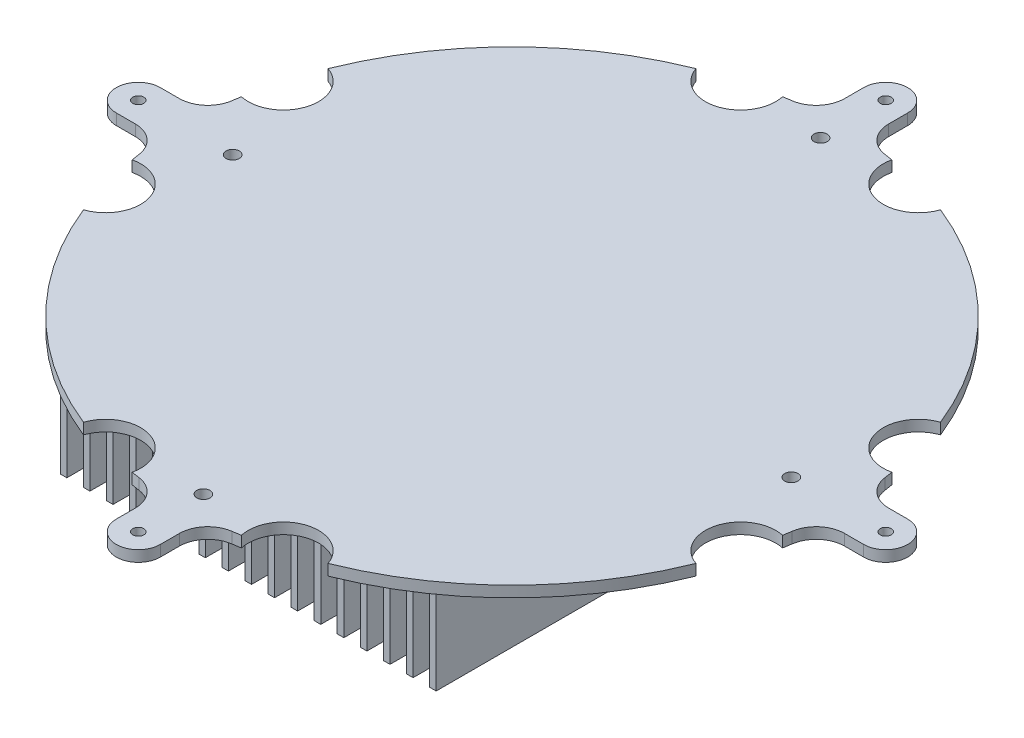
SolidWorks part; units mm, degrees
material "1060 Alloy"
ref_plane "Front Plane" through (0, 0, 0) normal (0, 0, 1) x (1, 0, 0)
ref_plane "Top Plane" through (0, 0, 0) normal (0, 1, 0) x (1, 0, 0)
ref_plane "Right Plane" through (0, 0, 0) normal (1, 0, 0) x (0, 0, -1)
sketch "Sketch3" plane through (0, 0, 0) normal (0, 1, 0) x (1, 0, 0)
  line L0 (0, 0) -> (211.9111, 0) construction
  line L1 (0, 0) -> (-205.2426, 0) construction
  line L2 (0, 0) -> (0, 170) construction
  line L3 (0, 0) -> (0, -200) construction
  line L4 (161.3691, 10) -> (170, 10)
  line L5 (161.3691, -10) -> (170, -10)
  line L6 (-10, 161.3691) -> (-10, 170)
  line L7 (10, 161.3691) -> (10, 170)
  line L8 (10, -161.3691) -> (10, -170)
  line L9 (-10, -161.3691) -> (-10, -170)
  line L10 (-161.3691, -10) -> (-170, -10)
  line L11 (-161.3691, 10) -> (-170, 10)
  arc A0 (-21.1656, 148.4992) -> (-148.4992, 21.1656) centre (0, 0) ccw
  circle A1 centre (0, 170) radius 2.5
  arc A2 (-10, 170) -> (10, 170) centre (0, 170) cw
  arc A3 (10, 161.3691) -> (21.1656, 148.4992) centre (23, 161.3691) ccw
  arc A4 (-10, 161.3691) -> (-21.1656, 148.4992) centre (-23, 161.3691) cw
  arc A5 (170, 10) -> (170, -10) centre (170, 0) cw
  arc A6 (161.3691, 10) -> (148.4992, 21.1656) centre (161.3691, 23) cw
  circle A7 centre (170, 0) radius 2.5
  arc A8 (161.3691, -10) -> (148.4992, -21.1656) centre (161.3691, -23) ccw
  arc A9 (10, -170) -> (-10, -170) centre (0, -170) cw
  arc A10 (10, -161.3691) -> (21.1656, -148.4992) centre (23, -161.3691) cw
  circle A11 centre (0, -170) radius 2.5
  arc A12 (-10, -161.3691) -> (-21.1656, -148.4992) centre (-23, -161.3691) ccw
  arc A13 (-170, -10) -> (-170, 10) centre (-170, 0) cw
  arc A14 (-161.3691, -10) -> (-148.4992, -21.1656) centre (-161.3691, -23) cw
  circle A15 centre (-170, 0) radius 2.5
  arc A16 (-161.3691, 10) -> (-148.4992, 21.1656) centre (-161.3691, 23) ccw
  arc A17 (-148.4992, -21.1656) -> (-21.1656, -148.4992) centre (0, 0) ccw
  arc A18 (148.4992, 21.1656) -> (21.1656, 148.4992) centre (0, 0) ccw
  arc A19 (21.1656, -148.4992) -> (148.4992, -21.1656) centre (0, 0) ccw
  point P53 (0, 0)
  dimension "D1" = 300
  dimension "D4" = 5
  dimension "D2" = 4
extrude "Boss-Extrude4" add sketch "Sketch3" against normal blind 5
sketch "Sketch4" plane through (0, -5, 0) normal (0, -1, 0) x (1, 0, 0)
  line L0 (0, 0) -> (0, -192.7937) construction
  line L1 (0, 0) -> (0, 216.5128) construction
  line L2 (0, 0) -> (-235.9747, 0) construction
  line L3 (0, 0) -> (242.3846, 0) construction
  line L4 (1.5, -120) -> (-1.5, -120)
  line L5 (1.5, -120) -> (1.5, 120)
  line L6 (-1.5, -120) -> (-1.5, 120)
  line L7 (1.5, 120) -> (-1.5, 120)
  line L8 (12, -120) -> (12, 120)
  line L9 (9, -120) -> (9, 120)
  line L10 (12, 120) -> (9, 120)
  line L11 (12, -120) -> (9, -120)
  line L12 (22.5, -120) -> (22.5, 120)
  line L13 (19.5, -120) -> (19.5, 120)
  line L14 (22.5, 120) -> (19.5, 120)
  line L15 (22.5, -120) -> (19.5, -120)
  line L16 (33, -120) -> (33, 120)
  line L17 (30, -120) -> (30, 120)
  line L18 (33, 120) -> (30, 120)
  line L19 (33, -120) -> (30, -120)
  line L20 (43.5, -120) -> (43.5, 120)
  line L21 (40.5, -120) -> (40.5, 120)
  line L22 (43.5, 120) -> (40.5, 120)
  line L23 (43.5, -120) -> (40.5, -120)
  line L24 (54, -120) -> (54, 120)
  line L25 (51, -120) -> (51, 120)
  line L26 (54, 120) -> (51, 120)
  line L27 (54, -120) -> (51, -120)
  line L28 (64.5, -120) -> (64.5, 120)
  line L29 (61.5, -120) -> (61.5, 120)
  line L30 (64.5, 120) -> (61.5, 120)
  line L31 (64.5, -120) -> (61.5, -120)
  line L32 (75, -120) -> (75, 120)
  line L33 (72, -120) -> (72, 120)
  line L34 (75, 120) -> (72, 120)
  line L35 (75, -120) -> (72, -120)
  line L36 (85.5, -120) -> (85.5, 120)
  line L37 (82.5, -120) -> (82.5, 120)
  line L38 (85.5, 120) -> (82.5, 120)
  line L39 (85.5, -120) -> (82.5, -120)
  line L40 (-85.5, -120) -> (-82.5, -120)
  line L41 (-85.5, 120) -> (-82.5, 120)
  line L42 (-82.5, -120) -> (-82.5, 120)
  line L43 (-85.5, -120) -> (-85.5, 120)
  line L44 (-75, -120) -> (-72, -120)
  line L45 (-75, 120) -> (-72, 120)
  line L46 (-72, -120) -> (-72, 120)
  line L47 (-75, -120) -> (-75, 120)
  line L48 (-64.5, -120) -> (-61.5, -120)
  line L49 (-64.5, 120) -> (-61.5, 120)
  line L50 (-61.5, -120) -> (-61.5, 120)
  line L51 (-64.5, -120) -> (-64.5, 120)
  line L52 (-54, -120) -> (-51, -120)
  line L53 (-54, 120) -> (-51, 120)
  line L54 (-51, -120) -> (-51, 120)
  line L55 (-54, -120) -> (-54, 120)
  line L56 (-43.5, -120) -> (-40.5, -120)
  line L57 (-43.5, 120) -> (-40.5, 120)
  line L58 (-40.5, -120) -> (-40.5, 120)
  line L59 (-43.5, -120) -> (-43.5, 120)
  line L60 (-33, -120) -> (-30, -120)
  line L61 (-33, 120) -> (-30, 120)
  line L62 (-30, -120) -> (-30, 120)
  line L63 (-33, -120) -> (-33, 120)
  line L64 (-22.5, -120) -> (-19.5, -120)
  line L65 (-22.5, 120) -> (-19.5, 120)
  line L66 (-19.5, -120) -> (-19.5, 120)
  line L67 (-22.5, -120) -> (-22.5, 120)
  line L68 (-12, -120) -> (-9, -120)
  line L69 (-12, 120) -> (-9, 120)
  line L70 (-9, -120) -> (-9, 120)
  line L71 (-12, -120) -> (-12, 120)
  point P8 (-1.5, 0)
  point P11 (1.5, 0)
  dimension "D1" = 120
  dimension "D2" = 1.5
  dimension "D4" = 7.5
  dimension "D3" = 9
extrude "Boss-Extrude5" add sketch "Sketch4" along normal blind 40
sketch "Sketch7" plane through (0, 0, 0) normal (0, 1, 0) x (1, 0, 0)
  line L0 (0, 0) -> (0, 199.2983) construction
  line L1 (180, 0) -> (-209.1437, 0) construction
  line L2 (0, 0) -> (0, -219.846) construction
  arc A0 (170, -10) -> (170, 10) centre (170, 0) ccw construction
  circle A1 centre (-127.0882, 0) radius 3
  circle A2 centre (0, 140.3779) radius 3
  circle A3 centre (0, -140.3779) radius 3
  circle A4 centre (127.0882, 0) radius 3
extrude "Cut-Extrude1" cut sketch "Sketch7" against normal blind 10
sketch "Sketch8" plane through (0, 0, 0) normal (0, 1, 0) x (1, 0, 0)
  line L0 (0, -180) -> (0, 180) construction
  line L1 (180, 0) -> (-180, 0) construction
  arc A0 (-10, -170) -> (10, -170) centre (0, -170) ccw construction
  arc A1 (10, 170) -> (-10, 170) centre (0, 170) ccw construction
  arc A2 (170, -10) -> (170, 10) centre (170, 0) ccw construction
  arc A3 (-170, 10) -> (-170, -10) centre (-170, 0) ccw construction
  arc A4 (21.1656, -148.4992) -> (148.4992, -21.1656) centre (0, 0) ccw construction
  arc A5 (24.8498, -147.9273) -> (55.6196, -139.3071) centre (0, 0) ccw
  arc A6 (55.6196, -139.3071) -> (24.8498, -147.9273) centre (40.4649, -144.4389) ccw
  arc A7 (-55.6196, -139.3071) -> (-24.8498, -147.9273) centre (-40.4649, -144.4389) cw
  arc A8 (-139.3071, -55.6196) -> (-147.9273, -24.8498) centre (-144.4389, -40.4649) ccw
  arc A9 (-139.3071, 55.6196) -> (-147.9273, 24.8498) centre (-144.4389, 40.4649) cw
  arc A10 (-55.6196, 139.3071) -> (-24.8498, 147.9273) centre (-40.4649, 144.4389) ccw
  arc A11 (55.6196, 139.3071) -> (24.8498, 147.9273) centre (40.4649, 144.4389) cw
  arc A12 (139.3071, 55.6196) -> (147.9273, 24.8498) centre (144.4389, 40.4649) ccw
  arc A13 (139.3071, -55.6196) -> (147.9273, -24.8498) centre (144.4389, -40.4649) cw
  arc A14 (-21.1656, 148.4992) -> (-148.4992, 21.1656) centre (0, 0) ccw construction
  arc A15 (-24.8498, 147.9273) -> (-55.6196, 139.3071) centre (0, 0) ccw
  arc A16 (148.4992, 21.1656) -> (21.1656, 148.4992) centre (0, 0) ccw construction
  arc A17 (-148.4992, -21.1656) -> (-21.1656, -148.4992) centre (0, 0) ccw construction
  arc A18 (147.9273, 24.8498) -> (139.3071, 55.6196) centre (0, 0) ccw
  arc A19 (-147.9273, -24.8498) -> (-139.3071, -55.6196) centre (0, 0) ccw
  arc A20 (139.3071, -55.6196) -> (147.9273, -24.8498) centre (0, 0) ccw
  arc A21 (-55.6196, -139.3071) -> (-24.8498, -147.9273) centre (0, 0) ccw
  arc A22 (-139.3071, 55.6196) -> (-147.9273, 24.8498) centre (0, 0) ccw
  arc A23 (55.6196, 139.3071) -> (24.8498, 147.9273) centre (0, 0) ccw
  point P38 (0, 0)
  dimension "D1" = 4
extrude "Cut-Extrude2" cut sketch "Sketch8" against normal blind 10
